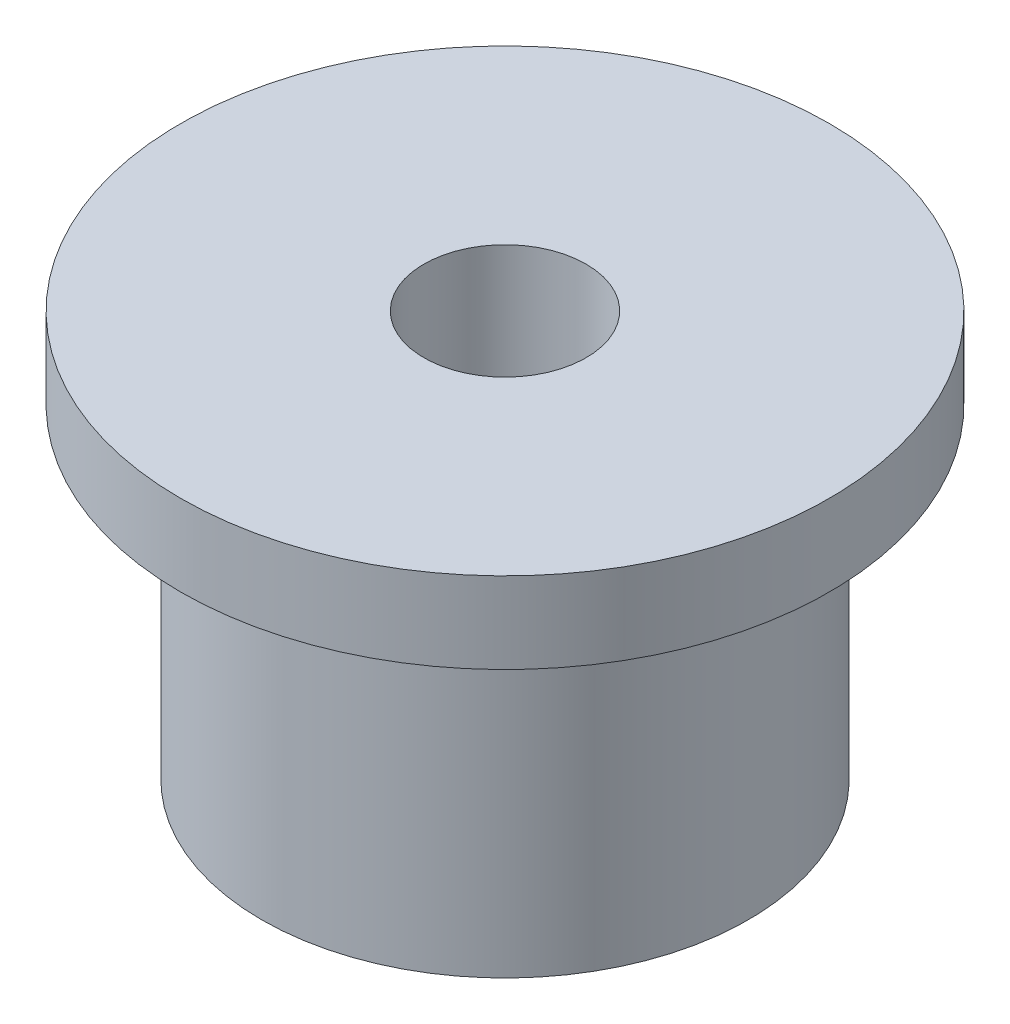
SolidWorks part; units mm, degrees
ref_plane "Front Plane" through (0, 0, 0) normal (0, 0, 1) x (1, 0, 0)
ref_plane "Top Plane" through (0, 0, 0) normal (0, 1, 0) x (1, 0, 0)
ref_plane "Right Plane" through (0, 0, 0) normal (1, 0, 0) x (0, 0, -1)
sketch "Sketch1" plane through (0, 0, 0) normal (0, 0, 1) x (1, 0, 0)
  line L0 (0, 0) -> (0, 132.5722) construction
  line L1 (25, 0) -> (25, 125)
  line L2 (25, 125) -> (100, 125)
  line L3 (100, 125) -> (100, 100)
  line L4 (100, 100) -> (75, 100)
  line L5 (75, 100) -> (75, 0)
  line L6 (75, 0) -> (25, 0)
  dimension "D1" = 75
  dimension "D2" = 25
  dimension "D3" = 125
  dimension "D4" = 25
  dimension "D5" = 100
revolve "Revolve1" add sketch "Sketch1" angle 360 about L0
